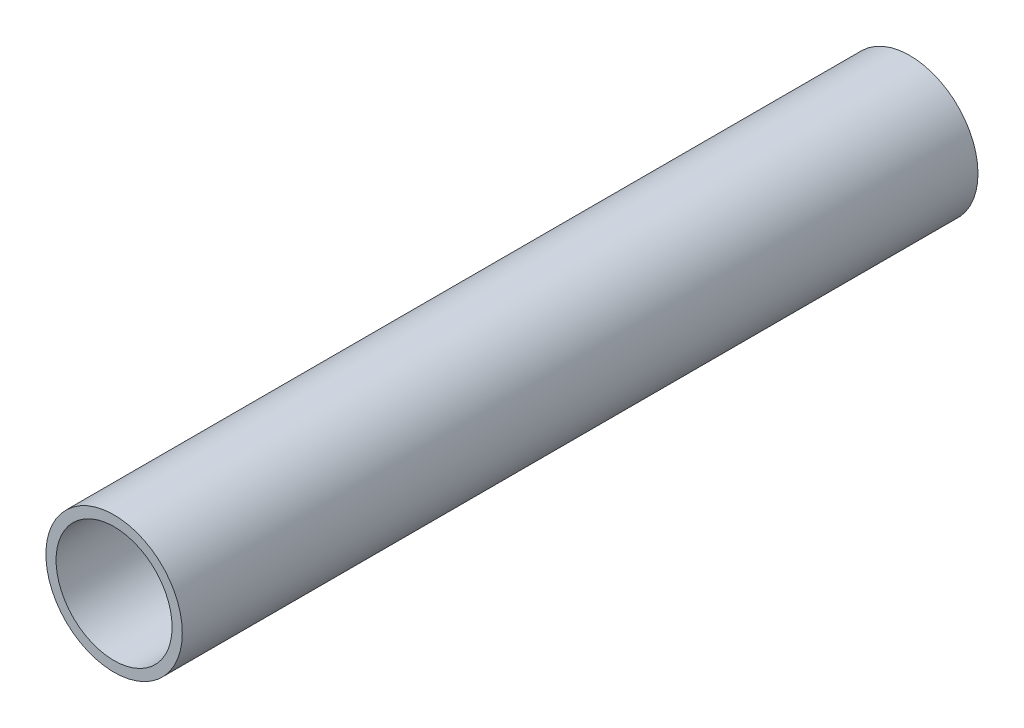
SolidWorks part; units mm, degrees
material "6061 Alloy"
ref_plane "XY" through (0, 0, 0) normal (0, 0, 1) x (1, 0, 0)
ref_plane "XZ" through (0, 0, 0) normal (0, 1, 0) x (1, 0, 0)
ref_plane "YZ" through (0, 0, 0) normal (1, 0, 0) x (0, 0, -1)
sketch "Sketch1" plane through (0, 0, 0) normal (0, 0, 1) x (1, 0, 0)
  circle A0 centre (0, 0) radius 4.7625
  circle A1 centre (0, 0) radius 4.0513
  dimension "D1" = 8.1026
  dimension "D2" = 9.525
extrude "Extrude1" add sketch "Sketch1" along normal mid plane 55.5625
